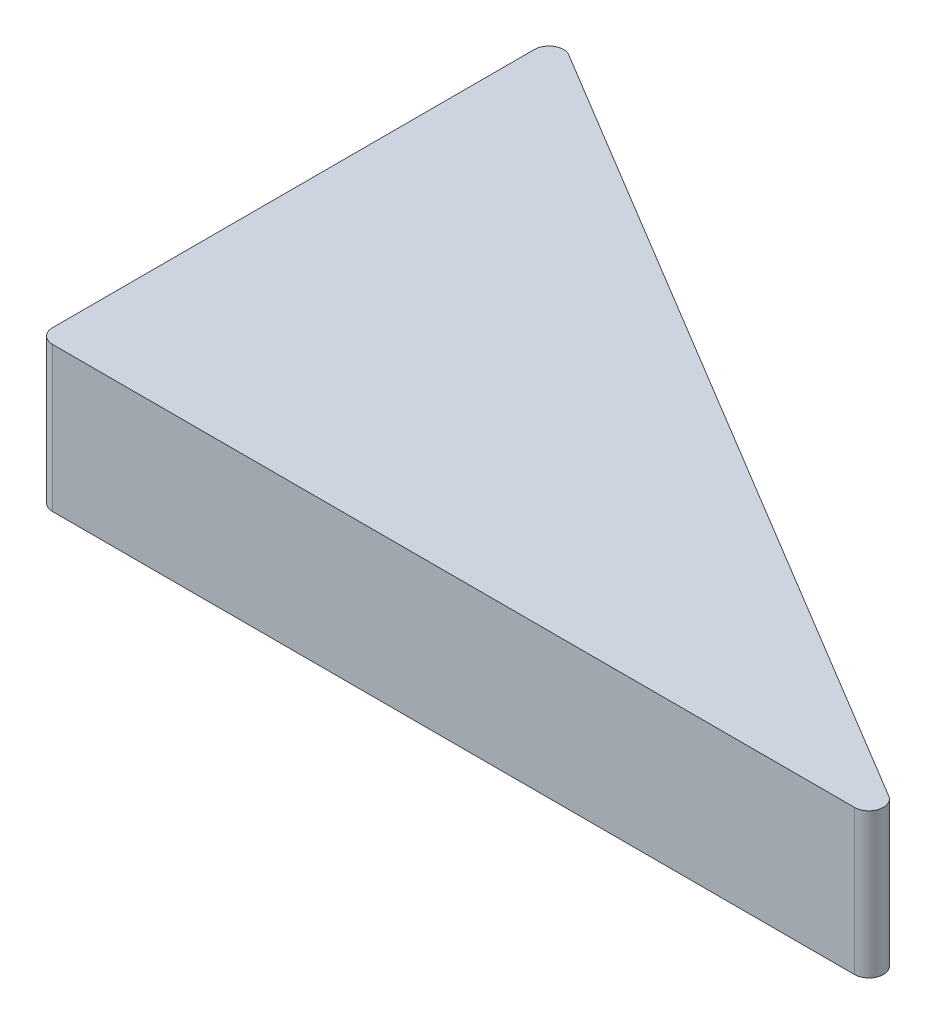
SolidWorks part; units mm, degrees
ref_plane "Front Plane" through (0, 0, 0) normal (0, 0, 1) x (1, 0, 0)
ref_plane "Top Plane" through (0, 0, 0) normal (0, 1, 0) x (1, 0, 0)
ref_plane "Right Plane" through (0, 0, 0) normal (1, 0, 0) x (0, 0, -1)
sketch "Sketch1" plane through (0, 0, 0) normal (0, 1, 0) x (1, 0, 0)
  line L0 (0, 1) -> (0, 34.2879)
  line L1 (1.5151, 35.1451) -> (56.9095, 1.8571)
  line L2 (56.3944, 0) -> (1, 0)
  arc A0 (56.9095, 1.8571) -> (56.3944, 0) centre (56.3944, 1) cw
  arc A1 (0, 1) -> (1, 0) centre (1, 1) ccw
  arc A2 (0, 34.2879) -> (1.5151, 35.1451) centre (1, 34.2879) cw
  point P6 (60, 0)
  point P9 (0, 0)
  point P12 (0, 36.0555)
  dimension "D3" = 1
  dimension "D1" = 60
  dimension "D2" = 70
extrude "Boss-Extrude1" add sketch "Sketch1" along normal blind 10
